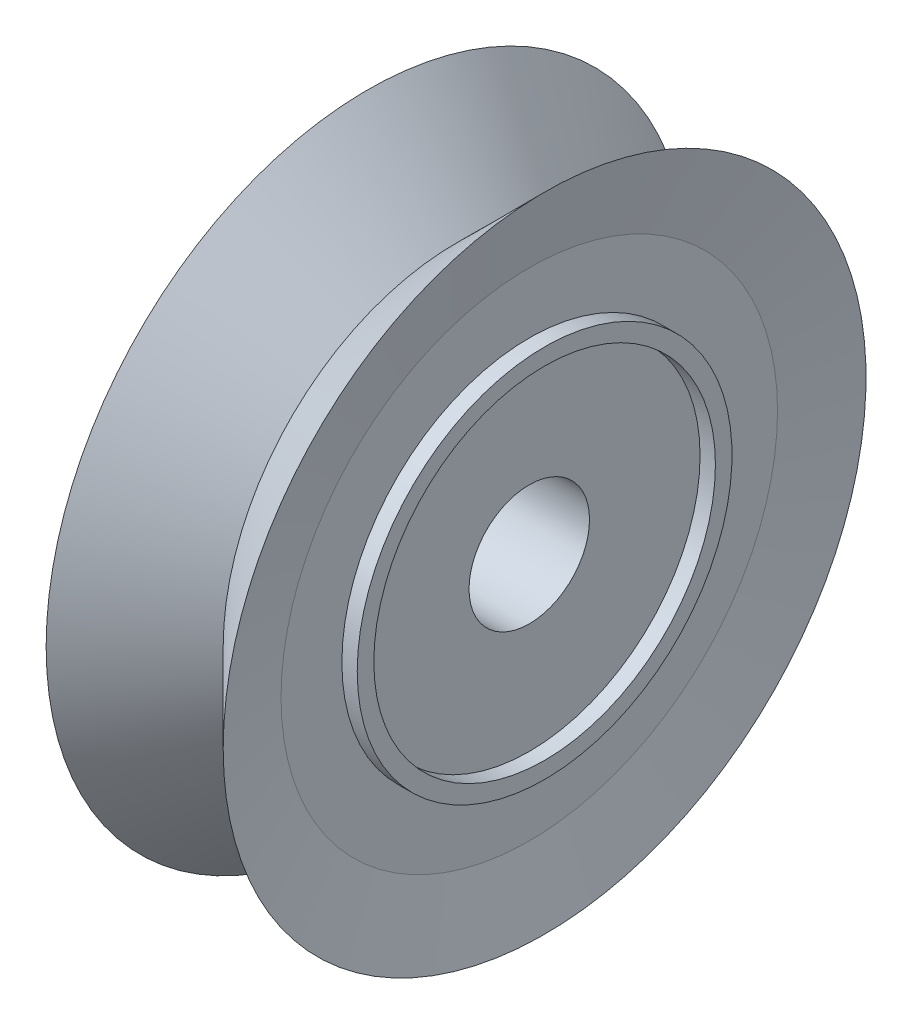
SolidWorks part; units mm, degrees
ref_plane "Front Plane" through (0, 0, 0) normal (0, 0, 1) x (1, 0, 0)
ref_plane "Top Plane" through (0, 0, 0) normal (0, 1, 0) x (1, 0, 0)
ref_plane "Right Plane" through (0, 0, 0) normal (1, 0, 0) x (0, 0, -1)
sketch "Sketch1" plane through (0, 0, 0) normal (0, 1, 0) x (1, 0, 0)
  line L0 (-26.9803, 7.3676) -> (-25.274, 9.0739)
  line L1 (-23.8635, 13.5628) -> (-23.3488, 13.5628) construction
  line L2 (-26.9803, 9.951) -> (-26.9803, 10.2708)
  line L3 (-26.9803, 7.3676) -> (-26.6846, 8.7782)
  line L4 (-26.6846, 8.7782) -> (-26.6846, 9.951)
  line L5 (-26.6846, 9.951) -> (-26.9803, 9.951)
  line L6 (-26.9803, 9.951) -> (-26.9803, 10.2708)
  line L7 (-26.9803, 10.2708) -> (-26.6846, 10.2708)
  line L8 (-26.6846, 10.2708) -> (-26.6846, 13.5628)
  line L9 (-26.6846, 13.5628) -> (-23.8635, 13.5628)
  line L11 (-23.8635, 10.2708) -> (-23.8635, 13.5628)
  line L12 (-23.5678, 10.2708) -> (-23.8635, 10.2708)
  line L13 (-23.5678, 9.951) -> (-23.5678, 10.2708)
  line L14 (-23.8635, 9.951) -> (-23.5678, 9.951)
  line L15 (-23.8635, 8.7782) -> (-23.8635, 9.951)
  line L16 (-23.5678, 7.3676) -> (-23.8635, 8.7782)
  line L17 (-23.5678, 9.951) -> (-23.5678, 10.2708)
  line L18 (-23.5678, 7.3676) -> (-25.274, 9.0739)
  line L19 (-25.274, 13.5628) -> (-25.274, 102.684) construction
  dimension "D1" = 2.8211
revolve "Revolve1" add sketch "Sketch1" angle 360 about L1
sketch "Sketch2" plane through (-26.6846, 0, 0) normal (-1, 0, 0) x (0, 0, 1)
  circle A0 centre (-13.5628, 0) radius 1.1608
extrude "Cut-Extrude1" cut sketch "Sketch2" against normal blind 7.62
